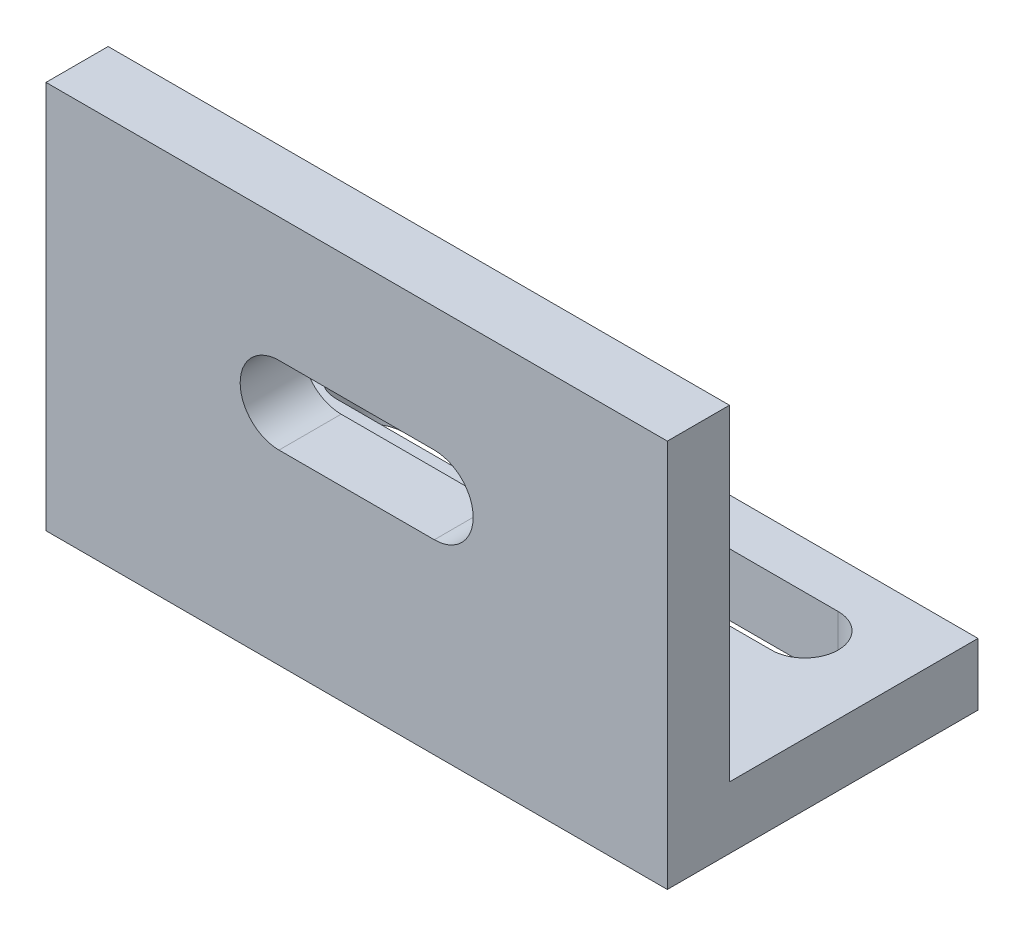
SolidWorks part; units mm, degrees
ref_plane "Front Plane" through (0, 0, 0) normal (0, 0, 1) x (1, 0, 0)
ref_plane "Top Plane" through (0, 0, 0) normal (0, 1, 0) x (1, 0, 0)
ref_plane "Right Plane" through (0, 0, 0) normal (1, 0, 0) x (0, 0, -1)
sketch "Sketch1" plane through (0, 0, 0) normal (0, 1, 0) x (1, 0, 0)
  line L1 (-49.2593, 12.8889) -> (-9.2593, 12.8889)
  line L2 (-49.2593, 12.8889) -> (-49.2593, -7.1111)
  line L4 (-9.2593, 12.8889) -> (-9.2593, -7.1111)
  line L5 (-49.2593, 12.8889) -> (-9.2593, -7.1111) construction
  line L6 (-49.2593, -7.1111) -> (-9.2593, 12.8889) construction
  line L13 (-49.2593, -7.1111) -> (-9.2593, -7.1111)
  line L14 (-49.2593, -7.1111) -> (-49.2593, -3.073)
  line L16 (-9.2593, -7.1111) -> (-9.2593, -3.073)
  point P4 (-29.2593, 2.8889)
  dimension "D1" = 40
  dimension "D2" = 20
extrude "Boss-Extrude1" add sketch "Sketch1" along normal blind 4 contours L2 L13 L4 L1
sketch "Sketch5" plane through (0, 4, 0) normal (0, 1, 0) x (1, 0, 0)
  line L0 (-9.2593, 12.8889) -> (-9.2593, -7.1111) construction
  line L1 (-49.2593, -7.1111) -> (-9.2593, -7.1111)
  line L2 (-49.2593, -7.1111) -> (-49.2593, -3.1111)
  line L3 (-49.2593, -3.1111) -> (-9.2593, -3.1111)
  line L4 (-9.2593, -7.1111) -> (-9.2593, -3.1111)
  line L5 (-49.2593, -7.1111) -> (-9.2593, -3.1111) construction
  line L6 (-49.2593, -3.1111) -> (-9.2593, -7.1111) construction
  point P4 (-29.2593, -5.1111)
  dimension "D1" = 4
extrude "Boss-Extrude2" add sketch "Sketch5" along normal blind 21
sketch "Sketch7" plane through (0, 4, 0) normal (0, 1, 0) x (1, 0, 0)
  line L0 (-49.2593, 12.8889) -> (-9.2593, 12.8889) construction
  line L4 (-15.2593, 7.7389) -> (-43.2593, 7.7389) construction
  line L7 (-15.2593, 5.5889) -> (-43.2593, 5.5889)
  line L8 (-15.2593, 9.8889) -> (-43.2593, 9.8889)
  line L9 (-9.2593, 12.8889) -> (-9.2593, -3.1111) construction
  line L10 (-49.2593, 12.8889) -> (-49.2593, -3.1111) construction
  arc A2 (-15.2593, 5.5889) -> (-15.2593, 9.8889) centre (-15.2593, 7.7389) ccw
  arc A3 (-43.2593, 9.8889) -> (-43.2593, 5.5889) centre (-43.2593, 7.7389) ccw
  point P4 (-29.2593, 12.8889)
  point P8 (-29.2593, 7.7389)
  dimension "D1" = 6
  dimension "D2" = 6
  dimension "D3" = 3
extrude "Cut-Extrude3" cut sketch "Sketch7" against normal blind 10
sketch "Sketch8" plane through (0, 0, 3.1111) normal (0, 0, -1) x (-1, 0, 0)
  line L13 (24.2593, 14.5) -> (34.2593, 14.5) construction
  line L14 (24.2593, 17) -> (34.2593, 17)
  line L15 (24.2593, 12) -> (34.2593, 12)
  arc A6 (24.2593, 17) -> (24.2593, 12) centre (24.2593, 14.5) ccw
  arc A7 (34.2593, 12) -> (34.2593, 17) centre (34.2593, 14.5) ccw
  point P1 (29.2593, 14.5)
extrude "Cut-Extrude5" cut sketch "Sketch8" against normal blind 10
